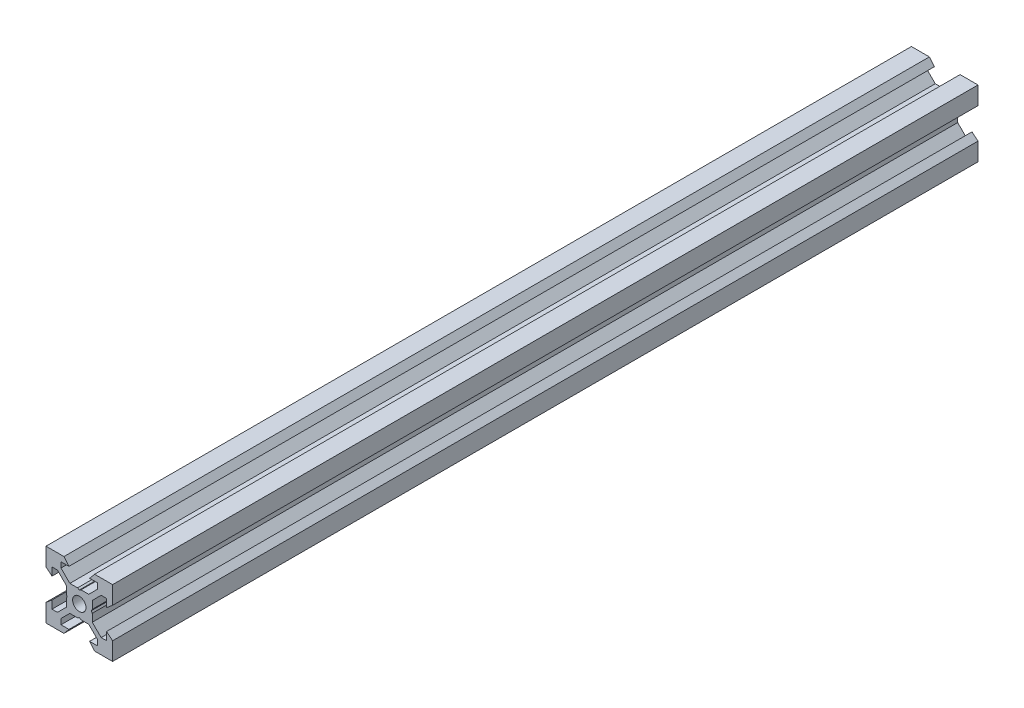
SolidWorks part; units mm, degrees
ref_plane "Front Plane" through (0, 0, 0) normal (0, 0, 1) x (1, 0, 0)
ref_plane "Top Plane" through (0, 0, 0) normal (0, 1, 0) x (1, 0, 0)
ref_plane "Right Plane" through (0, 0, 0) normal (1, 0, 0) x (0, 0, -1)
sketch "Sketch1" plane through (0, 0, 0) normal (0, 0, 1) x (1, 0, 0)
  line L0 (10, 10) -> (4.6104, 10) construction
  line L1 (10, 10) -> (10, 4.6104) construction
  line L2 (10, -10) -> (10, -4.6104) construction
  line L3 (10, -10) -> (4.6104, -10) construction
  line L4 (10, 10) -> (10, 4.6104)
  line L5 (6.5607, 5.5) -> (8.2, 5.5)
  line L6 (5.5, 8.2) -> (5.5, 6.5607)
  line L7 (10, 10) -> (4.6104, 10)
  line L8 (10, 10) -> (10, 4.6104)
  line L9 (6.5607, 5.5) -> (3.9, 2.8393)
  line L10 (5.5, 6.5607) -> (2.8393, 3.9)
  line L11 (10, 4.6104) -> (8.2, 3.1)
  line L12 (4.6104, 10) -> (3.1, 8.2)
  line L13 (8.2, 3.1) -> (8.2, 5.5)
  line L14 (3.1, 8.2) -> (5.5, 8.2)
  line L15 (-6.5607, 5.5) -> (-8.2, 5.5)
  line L16 (6.5607, -5.5) -> (8.2, -5.5)
  line L17 (3.1, -8.2) -> (5.5, -8.2)
  line L18 (8.2, -3.1) -> (8.2, -5.5)
  line L19 (4.6104, -10) -> (3.1, -8.2)
  line L20 (10, -4.6104) -> (8.2, -3.1)
  line L21 (0.5196, -3.9) -> (0, -3.6)
  line L22 (0.5196, 3.9) -> (0, 3.6)
  line L23 (3.6, 0) -> (3.9, -0.5196)
  line L24 (3.9, 0.5196) -> (3.6, 0)
  line L25 (3.9, 0.5196) -> (3.9, 2.8393)
  line L26 (2.8393, 3.9) -> (0.5196, 3.9)
  line L27 (3.9, -2.8393) -> (3.9, -0.5196)
  line L28 (2.8393, -3.9) -> (0.5196, -3.9)
  line L29 (5.5, -6.5607) -> (2.8393, -3.9)
  line L30 (6.5607, -5.5) -> (3.9, -2.8393)
  line L31 (10, -10) -> (10, -4.6104)
  line L32 (10, -10) -> (4.6104, -10)
  line L33 (5.5, -8.2) -> (5.5, -6.5607)
  line L34 (-6.5607, -5.5) -> (-8.2, -5.5)
  line L35 (10, -10) -> (10, -4.6104)
  line L36 (0, 0) -> (0, 8.2) construction
  line L37 (-10, -10) -> (-4.6104, -10) construction
  line L38 (-10, -10) -> (-10, -4.6104) construction
  line L39 (-10, 10) -> (-10, 4.6104) construction
  line L40 (-10, 10) -> (-4.6104, 10) construction
  line L41 (-10, -10) -> (-10, -4.6104)
  line L43 (-5.5, -8.2) -> (-5.5, -6.5607)
  line L44 (-10, -10) -> (-4.6104, -10)
  line L45 (-10, -10) -> (-10, -4.6104)
  line L46 (-6.5607, -5.5) -> (-3.9, -2.8393)
  line L47 (-5.5, -6.5607) -> (-2.8393, -3.9)
  line L48 (-2.8393, -3.9) -> (-0.5196, -3.9)
  line L49 (-3.9, -2.8393) -> (-3.9, -0.5196)
  line L50 (-2.8393, 3.9) -> (-0.5196, 3.9)
  line L51 (-3.9, 0.5196) -> (-3.9, 2.8393)
  line L52 (-3.9, 0.5196) -> (-3.6, 0)
  line L53 (-3.6, 0) -> (-3.9, -0.5196)
  line L54 (-0.5196, 3.9) -> (0, 3.6)
  line L55 (-0.5196, -3.9) -> (0, -3.6)
  line L56 (-10, -4.6104) -> (-8.2, -3.1)
  line L57 (-4.6104, -10) -> (-3.1, -8.2)
  line L58 (-8.2, -3.1) -> (-8.2, -5.5)
  line L59 (-3.1, -8.2) -> (-5.5, -8.2)
  line L60 (-10, -10) -> (10, -10) construction
  line L61 (-10, -10) -> (-10, 10) construction
  line L62 (-3.1, 8.2) -> (-5.5, 8.2)
  line L63 (-8.2, 3.1) -> (-8.2, 5.5)
  line L64 (-4.6104, 10) -> (-3.1, 8.2)
  line L65 (-10, 4.6104) -> (-8.2, 3.1)
  line L66 (-5.5, 6.5607) -> (-2.8393, 3.9)
  line L67 (-6.5607, 5.5) -> (-3.9, 2.8393)
  line L68 (-10, 10) -> (-10, 4.6104)
  line L69 (-10, 10) -> (-4.6104, 10)
  line L70 (-5.5, 8.2) -> (-5.5, 6.5607)
  line L71 (-10, 10) -> (10, 10) construction
  line L72 (-10, 10) -> (-10, 4.6104)
  line L73 (10, -10) -> (10, 10) construction
  line L74 (-10, -10) -> (10, 10) construction
  line L75 (-10, 10) -> (10, -10) construction
  circle A0 centre (0, 0) radius 2
  dimension "D7" = 4
  dimension "D1" = 20
  dimension "D2" = 5.3896
  dimension "D3" = 4.5
  dimension "D4" = 50
  dimension "D5" = 1.8
  dimension "D6" = 1.5104
  dimension "D8" = 5.5
  dimension "D9" = 120
  dimension "D10" = 0.3
  dimension "D11" = 2.3197
  dimension "D12" = 7.8
  dimension "D13" = 7.8
  dimension "D14" = 1.5
  dimension "D15" = 2.6607
extrude "Boss-Extrude1" add sketch "Sketch1" along normal mid plane 260 contours L70 L62 L64 L69 L68 L65 L63 L15 L67 L51 L52 L53 L49 L46 L34 L58 L56 L41 L44 L57 L59 L43 L47 L48 L55 L21 L28 L29 L33 L17 L19 L32 L31 L20 L18 L16 L30 L27 L23 L24 L25 L9 L5 L13 L11 L4 L7 L12 L14 L6 L10
